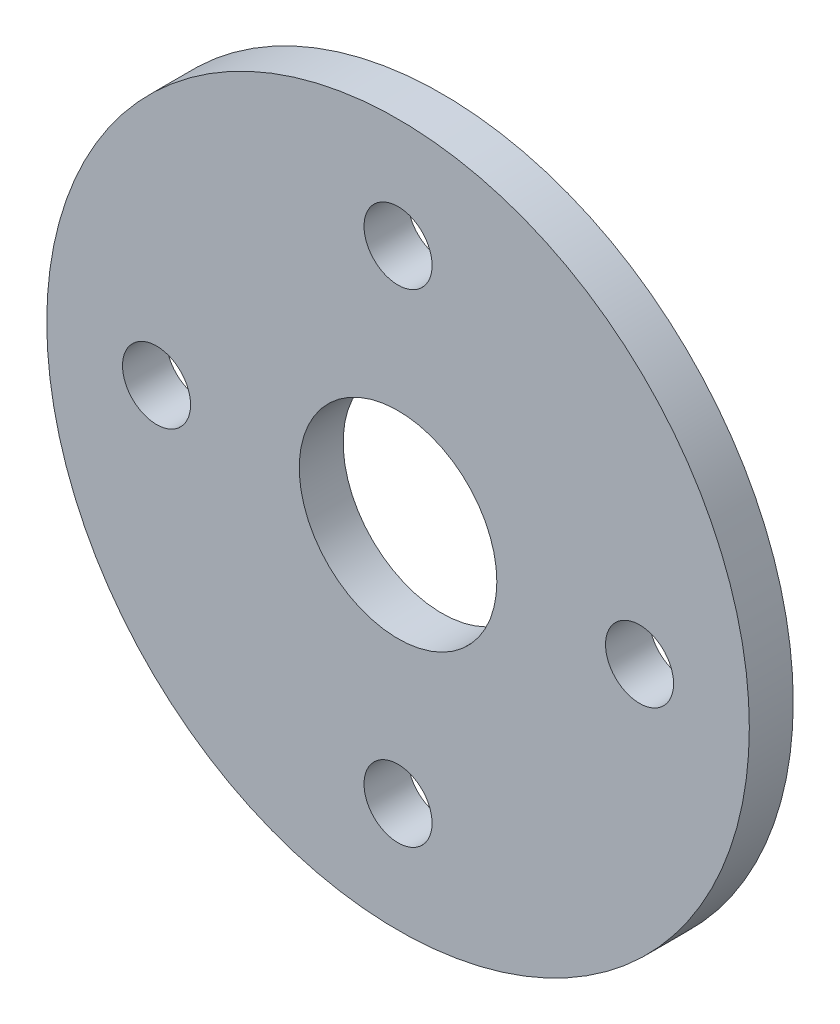
SolidWorks part; units mm, degrees
ref_plane "Front Plane" through (0, 0, 0) normal (0, 0, 1) x (1, 0, 0)
ref_plane "Top Plane" through (0, 0, 0) normal (0, 1, 0) x (1, 0, 0)
ref_plane "Right Plane" through (0, 0, 0) normal (1, 0, 0) x (0, 0, -1)
sketch "Sketch1" plane through (0, 0, 0) normal (0, 0, 1) x (1, 0, 0)
  circle A0 centre (0, 0) radius 4.5
  circle A1 centre (0, 0) radius 16
  circle A2 centre (0, 0) radius 11 construction
  circle A3 centre (0, 11) radius 1.55
  circle A4 centre (11, 0) radius 1.55
  circle A5 centre (0, -11) radius 1.55
  circle A6 centre (-11, 0) radius 1.55
  point P16 (0, 0)
  dimension "D1" = 32
  dimension "D2" = 9
  dimension "D3" = 22
  dimension "D4" = 3.1
  dimension "D5" = 4
extrude "Boss-Extrude1" add sketch "Sketch1" along normal blind 2
